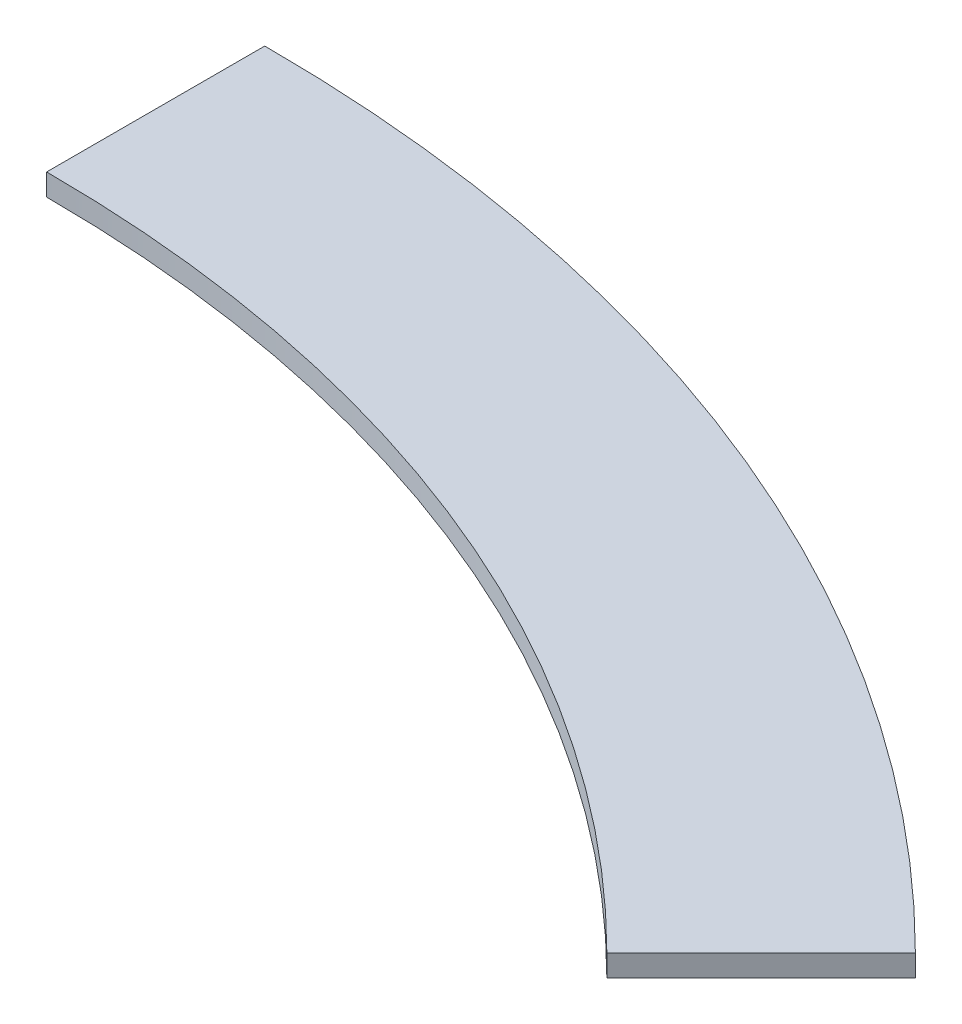
SolidWorks part; units mm, degrees
ref_plane "Front Plane" through (0, 0, 0) normal (0, 0, 1) x (1, 0, 0)
ref_plane "Top Plane" through (0, 0, 0) normal (0, 1, 0) x (1, 0, 0)
ref_plane "Right Plane" through (0, 0, 0) normal (1, 0, 0) x (0, 0, -1)
sketch "Sketch1" plane through (0, 0, 0) normal (0, 1, 0) x (1, 0, 0)
  line L0 (0, 0) -> (0, 620) construction
  line L1 (0, 620) -> (0, 720)
  line L2 (0, 0) -> (509.1169, 509.1169) construction
  line L3 (438.4062, 438.4062) -> (509.1169, 509.1169)
  arc A0 (0, 620) -> (438.4062, 438.4062) centre (0, 0) cw
  arc A1 (0, 720) -> (509.1169, 509.1169) centre (0, 0) cw
  dimension "D1" = 100
  dimension "D2" = 620
  dimension "D3" = 720
  dimension "D4" = 45
extrude "Boss-Extrude1" add sketch "Sketch1" along normal blind 10 contours A1 L1 A0 L3
